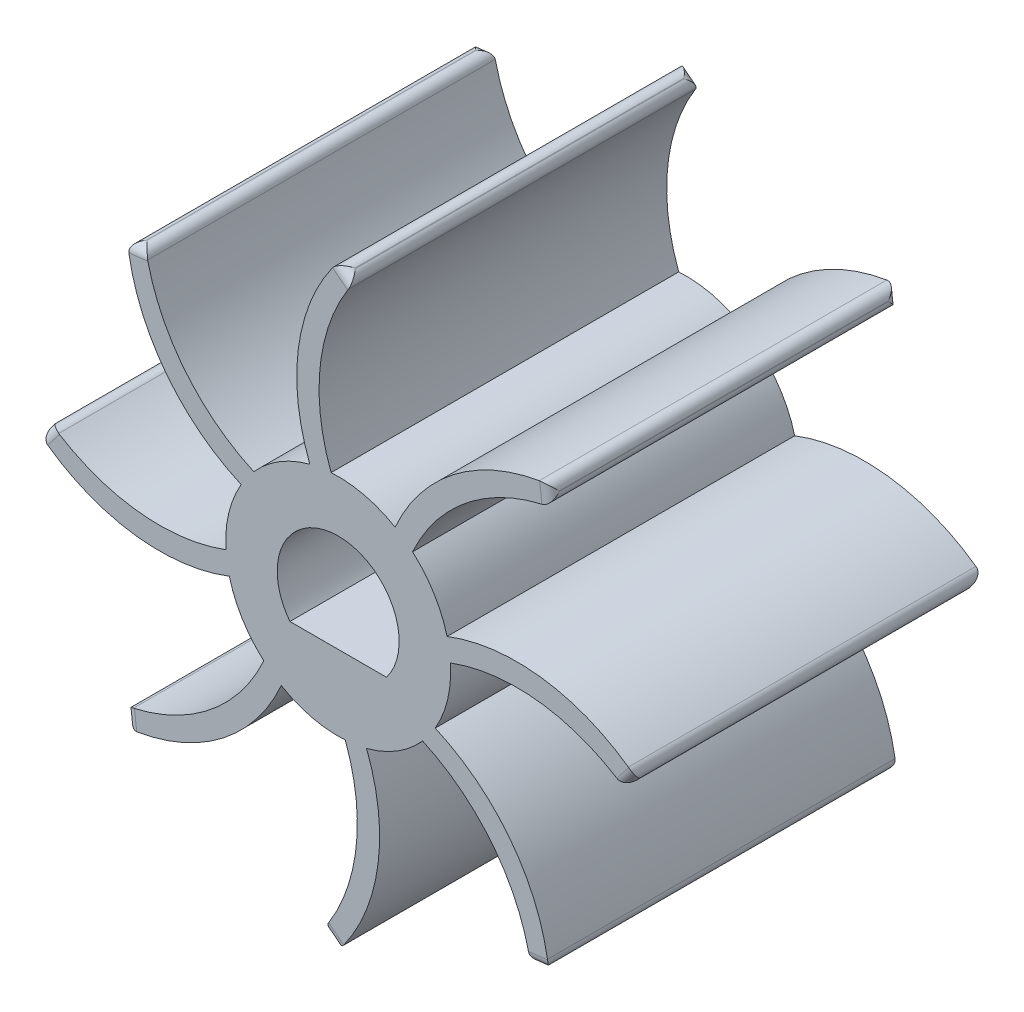
SolidWorks part; units mm, degrees
ref_plane "Front Plane" through (0, 0, 0) normal (0, 0, 1) x (1, 0, 0)
ref_plane "Top Plane" through (0, 0, 0) normal (0, 1, 0) x (1, 0, 0)
ref_plane "Right Plane" through (0, 0, 0) normal (1, 0, 0) x (0, 0, -1)
sketch "Sketch1" plane through (0, 0, 0) normal (0, 0, 1) x (1, 0, 0)
  line L0 (0, 24) -> (1.1772, 23.0703)
  line L1 (16.9706, 16.9706) -> (17.1456, 15.4808)
  line L2 (24, 0) -> (23.0703, -1.1772)
  line L3 (16.9706, -16.9706) -> (15.4808, -17.1456)
  line L4 (0, -24) -> (-1.1772, -23.0703)
  line L5 (-16.9706, -16.9706) -> (-17.1456, -15.4808)
  line L6 (-24, 0) -> (-23.0703, 1.1772)
  line L7 (-16.9706, 16.9706) -> (-15.4808, 17.1456)
  line L8 (-3.8883, -3) -> (3.8883, -3)
  circle A0 centre (0, 0) radius 9.0616
  arc A1 (0, 24) -> (-2.2834, 8.7692) centre (12.17, 14.3889) ccw
  arc A2 (1.1772, 23.0703) -> (-0.5713, 9.0436) centre (13.67, 14.3908) ccw
  arc A3 (16.9706, 16.9706) -> (4.5862, 7.8154) centre (18.78, 1.569) ccw
  arc A4 (17.1456, 15.4808) -> (5.9909, 6.7987) centre (19.8419, 0.5097) ccw
  arc A5 (24, 0) -> (8.7692, 2.2834) centre (14.3889, -12.17) ccw
  arc A6 (23.0703, -1.1772) -> (9.0436, 0.5713) centre (14.3908, -13.67) ccw
  arc A7 (16.9706, -16.9706) -> (7.8154, -4.5862) centre (1.569, -18.78) ccw
  arc A8 (15.4808, -17.1456) -> (6.7987, -5.9909) centre (0.5097, -19.8419) ccw
  arc A9 (0, -24) -> (2.2834, -8.7692) centre (-12.17, -14.3889) ccw
  arc A10 (-1.1772, -23.0703) -> (0.5713, -9.0436) centre (-13.67, -14.3908) ccw
  arc A11 (-16.9706, -16.9706) -> (-4.5862, -7.8154) centre (-18.78, -1.569) ccw
  arc A12 (-17.1456, -15.4808) -> (-5.9909, -6.7987) centre (-19.8419, -0.5097) ccw
  arc A13 (-24, 0) -> (-8.7692, -2.2834) centre (-14.3889, 12.17) ccw
  arc A14 (-23.0703, 1.1772) -> (-9.0436, -0.5713) centre (-14.3908, 13.67) ccw
  arc A15 (-16.9706, 16.9706) -> (-7.8154, 4.5862) centre (-1.569, 18.78) ccw
  arc A16 (-15.4808, 17.1456) -> (-6.7987, 5.9909) centre (-0.5097, 19.8419) ccw
  arc A17 (3.8883, -3) -> (-3.8883, -3) centre (0, 0) ccw
  point P53 (0, 0)
  dimension "D1" = 24
  dimension "D3" = 1.5
  dimension "D5" = 3
  dimension "D2" = 1.5
  dimension "D4" = 8
extrude "Boss-Extrude1" add sketch "Sketch1" along normal blind 28 contours A0 A17 L8 | A12 L5 A11 A0 | A14 L6 A13 A0 | A16 L7 A15 A0 | A2 L0 A1 A0 | A4 L1 A3 A0 | A6 L2 A5 A0 | A8 L3 A7 A0 | A10 L4 A9 A0
fillet "Fillet1" radius 0.75 32 edges at (-15.4808, 17.1456, 14) (-16.2257, 17.0581, 0) (-16.2257, 17.0581, 28) (-16.9706, 16.9706, 14) (-23.0703, 1.1772, 14) (-23.5352, 0.5886, 0) (-23.5352, 0.5886, 28) (-24, 0, 14) (-17.1456, -15.4808, 14) (-17.0581, -16.2257, 0) (-17.0581, -16.2257, 28) (-16.9706, -16.9706, 14) (-1.1772, -23.0703, 14) (-0.5886, -23.5352, 0) (-0.5886, -23.5352, 28) (0, -24, 14) (15.4808, -17.1456, 14) (16.2257, -17.0581, 0) (16.2257, -17.0581, 28) (16.9706, -16.9706, 14) (23.0703, -1.1772, 14) (23.5352, -0.5886, 0) (23.5352, -0.5886, 28) (24, 0, 14) (17.1456, 15.4808, 14) (17.0581, 16.2257, 0) (17.0581, 16.2257, 28) (16.9706, 16.9706, 14) (1.1772, 23.0703, 14) (0.5886, 23.5352, 0) (0.5886, 23.5352, 28) (0, 24, 14)
